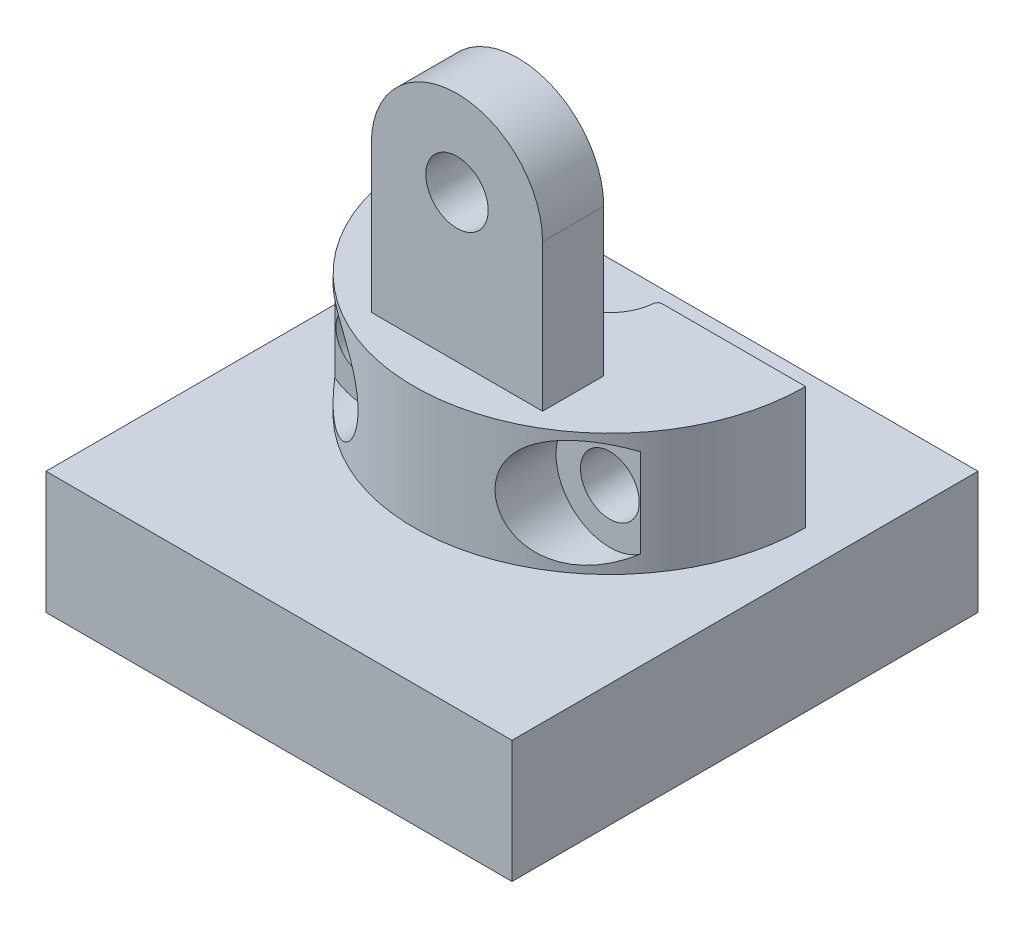
SolidWorks part; units mm, degrees
material "6061 Alloy"
ref_plane "Front Plane" through (0, 0, 0) normal (0, 0, 1) x (1, 0, 0)
ref_plane "Top Plane" through (0, 0, 0) normal (0, 1, 0) x (1, 0, 0)
ref_plane "Right Plane" through (0, 0, 0) normal (1, 0, 0) x (0, 0, -1)
sketch "Sketch1" plane through (0, 0, 0) normal (0, 1, 0) x (1, 0, 0)
  line L0 (1.96, 0) -> (8, 0)
  line L1 (-1.96, 0) -> (-8, 0)
  arc A0 (-8, 0) -> (8, 0) centre (0, 0) ccw
  arc A1 (1.96, 0) -> (-1.96, 0) centre (0, 0) cw
  dimension "D1" = 1.96
  dimension "D2" = 8
extrude "Boss-Extrude1" add sketch "Sketch1" along normal mid plane 5 contours L0 A0 L1 A1
sketch "Sketch2" plane through (0, 2.5, 0) normal (0, 1, 0) x (1, 0, 0)
  line L0 (3.5, -3.75) -> (-3.5, -3.75)
  line L1 (-3.5, -3.75) -> (-3.5, -6.25)
  line L2 (3.5, -6.25) -> (3.5, -3.75)
  line L3 (3.5, -6.25) -> (-3.5, -6.25)
  line L4 (1.96, 0) -> (8, 0) construction
  arc A0 (-1.96, 0) -> (1.96, 0) centre (0, 0) ccw construction
  dimension "D1" = 2.5
  dimension "D2" = 3.75
  dimension "D3" = 7
  dimension "D4" = 3.5
extrude "Boss-Extrude2" add sketch "Sketch2" along normal blind 9.5 contours L2 L0 L1 L3
sketch "Sketch3" plane through (0, 0, 3.75) normal (0, 0, -1) x (-1, 0, 0)
  line L0 (3.5, 12) -> (3.5, 2.5) construction
  line L1 (-3.5, 8.5) -> (-3.5, 14.8864)
  line L2 (-3.5, 14.8864) -> (0, 16.8092)
  line L3 (0, 16.8092) -> (3.5, 14.5)
  line L4 (3.5, 14.5) -> (3.5, 8.5)
  line L6 (-3.5, 12) -> (3.5, 12) construction
  line L7 (-3.5, 12) -> (-3.5, 2.5) construction
  arc A0 (3.5, 8.5) -> (-3.5, 8.5) centre (0, 8.5) ccw
extrude "Cut-Extrude1" cut sketch "Sketch3" against normal blind 9.5 contours L3 L4 A0 L1 L2
sketch "Sketch4" plane through (0, 0, 3.75) normal (0, 0, -1) x (-1, 0, 0)
  circle A0 centre (0, 8.5) radius 1.275
  dimension "D1" = 2.55
extrude "Cut-Extrude2" cut sketch "Sketch4" against normal blind 9.5
ref_plane "Plane1" through (0, 0, 7) normal (0, 0, -1) x (-1, 0, 0)
hole_wizard "CBORE for M2 SHCS1" positions "Sketch5" profile "Sketch7" counterbore size "M2" standard "ANSI Metric"
sketch "Sketch5" plane through (0, 0, 7) normal (0, 0, -1) x (-1, 0, 0)
  point P0 (-5, 0)
  point P2 (5, 0)
  dimension "D1" = 5
  dimension "D2" = 5
sketch "Sketch7" plane through (5, 0, 7) normal (1, 0, 0) x (0, -1, 0)
  line L0 (0, 0) -> (0, 7)
  line L1 (0, 7) -> (1.2, 7)
  line L3 (1.2, 7) -> (1.2, 2)
  line L4 (1.2, 2) -> (2.2, 2)
  line L5 (2.2, 2) -> (2.2, 0)
  line L7 (2.2, 0) -> (0, 0)
  line L11 (0, -6.35) -> (0, 107.95) construction
  dimension "Thru Hole Dia." = 2.4
  dimension "Thru Hole Depth" = 7
  dimension "C'Bore Dia." = 4.4
  dimension "C'Bore Depth" = 2
sketch "Sketch8" plane through (0, 0, 7) normal (0, 0, -1) x (-1, 0, 0)
  circle A0 centre (-5, 0) radius 2.2
  circle A1 centre (5, 0) radius 2.2
  arc A2 (-3.873, 1.8894) -> (-6.245, 1.8138) centre (-5, 0) ccw construction
  arc A3 (3.873, -1.8894) -> (6.245, -1.8138) centre (5, 0) ccw construction
extrude "Cut-Extrude3" cut sketch "Sketch8" against normal blind 9.5
sketch "Sketch9" plane through (0, 0, 0) normal (0, 0, 1) x (1, 0, 0)
  line L0 (0, 0.5) -> (-3, 2.5)
  line L1 (-1.96, 2.5) -> (-8, 2.5) construction
  line L2 (-3, 2.5) -> (0, 2.5)
  line L3 (0, 2.5) -> (0, 0.5)
  dimension "D1" = 3
  dimension "D2" = 2
sketch "Sketch10" plane through (0, 0, 0) normal (0, 0, -1) x (-1, 0, 0)
  line L0 (1.96, -2.5) -> (-1.96, -2.5)
sketch "Sketch11" plane through (0, -2.5, 0) normal (0, -1, 0) x (1, 0, 0)
  line L0 (-1.96, 0) -> (-8, 0) construction
  line L1 (9.525, 13.525) -> (-9.525, 13.525)
  line L2 (9.525, 13.525) -> (9.525, -5.525)
  line L3 (9.525, -5.525) -> (-9.525, -5.525)
  line L4 (-9.525, 13.525) -> (-9.525, -5.525)
  line L5 (9.525, 13.525) -> (-9.525, -5.525) construction
  line L6 (9.525, -5.525) -> (-9.525, 13.525) construction
  point P0 (0, 4)
  dimension "D1" = 19.05
  dimension "D2" = 19.05
  dimension "D3" = 4
extrude "Boss-Extrude3" add sketch "Sketch11" along normal blind 5
fillet "Fillet1" radius 0.2 2 edges at (-1.96, 0, 0) (1.96, 0, 0)
